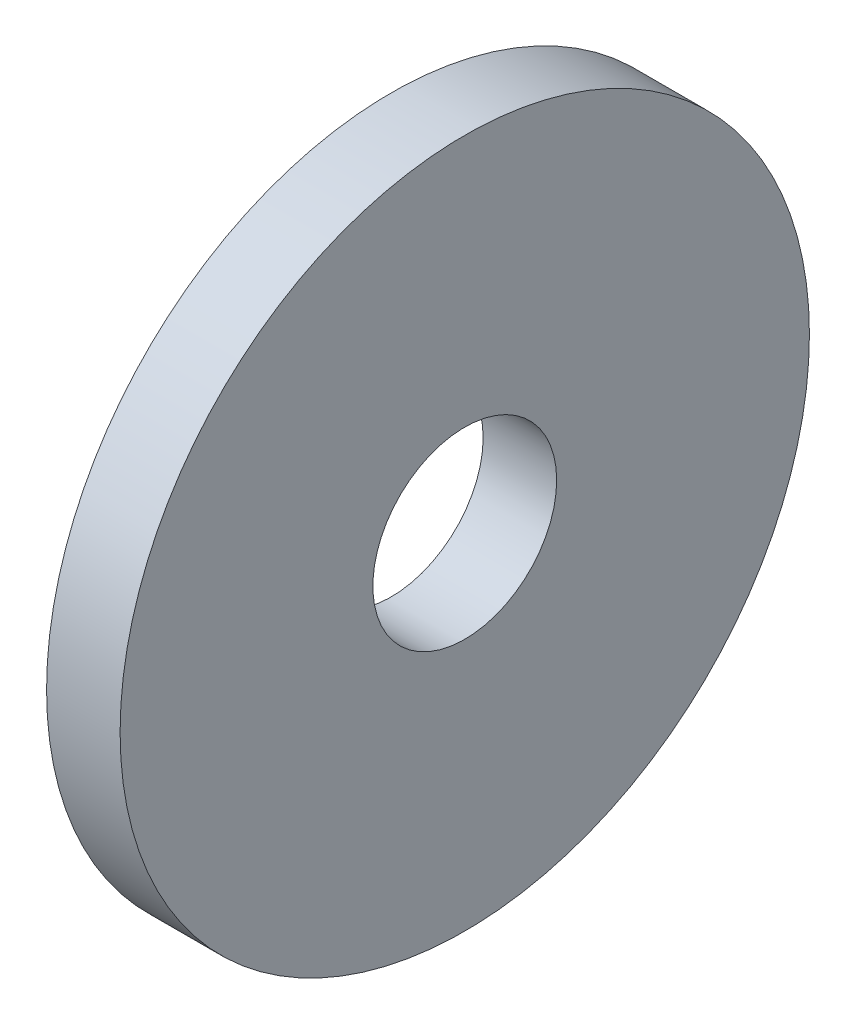
SolidWorks part; units mm, degrees
material "PVC Rigid"
ref_plane "Front Plane" through (0, 0, 0) normal (0, 0, 1) x (1, 0, 0)
ref_plane "Top Plane" through (0, 0, 0) normal (0, 1, 0) x (1, 0, 0)
ref_plane "Right Plane" through (0, 0, 0) normal (1, 0, 0) x (0, 0, -1)
sketch "Sketch1" plane through (0, 0, 0) normal (1, 0, 0) x (0, 0, -1)
  circle A0 centre (0, 0) radius 37.5
  dimension "D1" = 75
extrude "Boss-Extrude1" add sketch "Sketch1" along normal blind 8
sketch "Sketch2" plane through (8, 0, 0) normal (1, 0, 0) x (0, 0, -1)
  circle A0 centre (0, 0) radius 10
  dimension "D1" = 20
extrude "Cut-Extrude1" cut sketch "Sketch2" against normal through all
